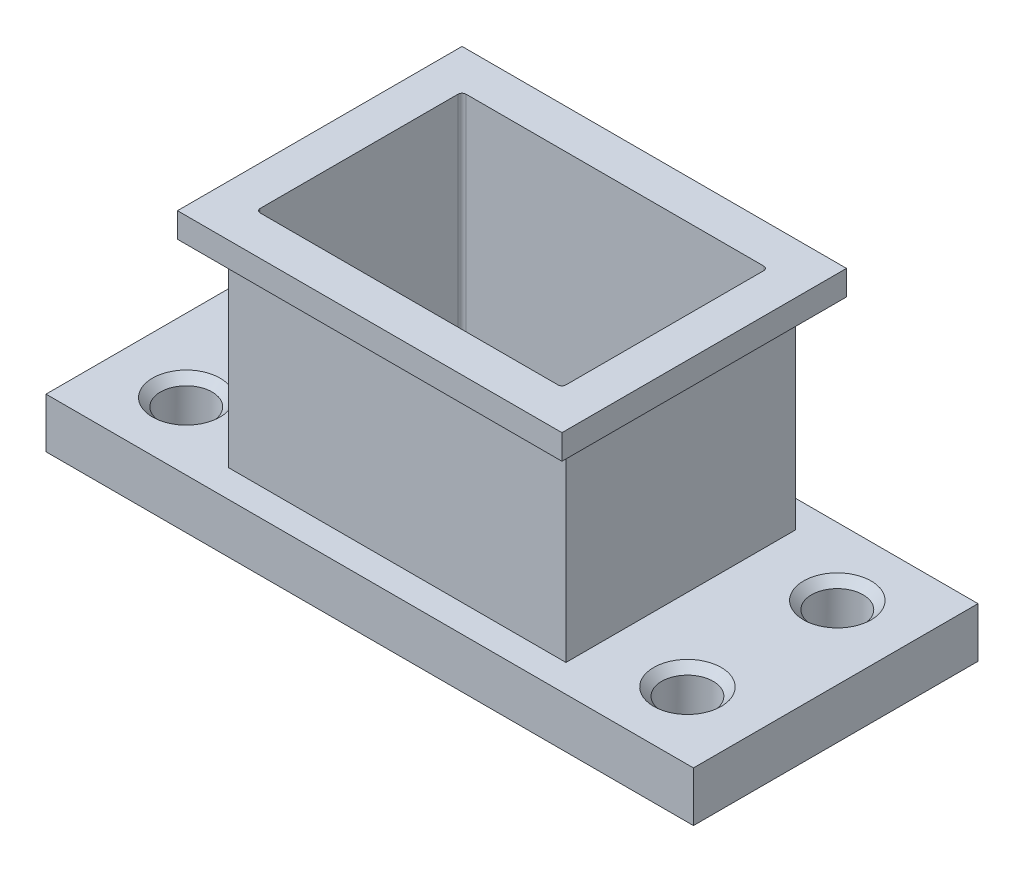
SolidWorks part; units mm, degrees
ref_plane "Front Plane" through (0, 0, 0) normal (0, 0, 1) x (1, 0, 0)
ref_plane "Top Plane" through (0, 0, 0) normal (0, 1, 0) x (1, 0, 0)
ref_plane "Right Plane" through (0, 0, 0) normal (1, 0, 0) x (0, 0, -1)
sketch "Sketch1" plane through (0, 0, 0) normal (0, 1, 0) x (1, 0, 0)
  line L1 (0, 0) -> (41.148, 0)
  line L2 (0, 0) -> (0, 18.0848)
  line L3 (0, 18.0848) -> (41.148, 18.0848)
  line L4 (41.148, 0) -> (41.148, 18.0848)
  line L5 (10.8585, 15.5829) -> (30.2895, 15.5829)
  line L6 (10.8585, 15.5829) -> (10.8585, 2.5019)
  line L7 (10.8585, 2.5019) -> (30.2895, 2.5019)
  line L8 (30.2895, 15.5829) -> (30.2895, 2.5019)
  dimension "D1" = 18.0848
  dimension "D2" = 41.148
  dimension "D3" = 10.8585
  dimension "D4" = 2.5019
  dimension "D5" = 2.5019
  dimension "D6" = 10.8585
  dimension "D7" = 19.431
  dimension "D8" = 13.081
extrude "Extrude1" add sketch "Sketch1" along normal blind 17.4498
sketch "Sketch2" plane through (0, 17.4498, 0) normal (0, 1, 0) x (-1, 0, 0)
  line L1 (0, 0) -> (-41.148, 0) construction
  line L2 (0, -18.0848) -> (-8.3566, -18.0848)
  line L3 (0, -18.0848) -> (0, 0)
  line L4 (0, 0) -> (-8.3566, 0)
  line L5 (-8.3566, -18.0848) -> (-8.3566, 0)
  line L7 (-41.148, -18.0848) -> (-32.7914, -18.0848)
  line L8 (-41.148, -18.0848) -> (-41.148, 0)
  line L9 (-41.148, 0) -> (-32.7914, 0)
  line L10 (-32.7914, -18.0848) -> (-32.7914, 0)
  dimension "D2" = 8.3566
  dimension "D1" = 8.3566
  dimension "D3" = 24.4348
extrude "Cut-Extrude1" cut sketch "Sketch2" against normal blind 14.2748
sketch "Sketch3" plane through (0, 17.4498, 0) normal (0, 1, 0) x (-1, 0, 0)
  line L1 (-31.2928, -16.3322) -> (-9.8552, -16.3322)
  line L2 (-31.2928, -16.3322) -> (-31.2928, -1.7526)
  line L3 (-31.2928, -1.7526) -> (-9.8552, -1.7526)
  line L4 (-8.3566, 0) -> (-32.7914, 0)
  line L5 (-32.7914, 0) -> (-32.7914, -18.0848)
  line L6 (-32.7914, -18.0848) -> (-8.3566, -18.0848)
  line L7 (-8.3566, -18.0848) -> (-8.3566, 0)
  line L8 (-8.3566, 0) -> (-32.7914, 0)
  line L9 (-32.7914, 0) -> (-32.7914, -18.0848)
  line L10 (-32.7914, -18.0848) -> (-8.3566, -18.0848)
  line L11 (-8.3566, -18.0848) -> (-8.3566, 0)
  line L12 (-9.8552, -16.3322) -> (-9.8552, -1.7526)
  dimension "D2" = 1.4986
  dimension "D3" = 1.4986
  dimension "D4" = 21.4376
  dimension "D5" = 1.7526
  dimension "D6" = 1.7526
  dimension "D7" = 14.5796
  dimension "D1" = 0
extrude "Cut-Extrude2" cut sketch "Sketch3" against normal up to surface (12.7 mm away) from offset 1.5748 up to face at (36.9697, 3.175, -9.0424) offset against normal yes
sketch "Sketch4" plane through (0, 3.175, 0) normal (0, 1, 0) x (-1, 0, 0)
  line L0 (0, -18.0848) -> (0, 0) construction
  line L1 (0, 0) -> (-41.148, 0) construction
  line L2 (-41.148, -18.0848) -> (0, -18.0848) construction
  line L3 (-41.148, 0) -> (-41.148, -18.0848) construction
  circle A0 centre (-36.4998, -13.7922) radius 1.6383
  circle A1 centre (-36.4998, -4.2672) radius 1.6383
  circle A2 centre (-4.6482, -4.2672) radius 1.6383
  circle A3 centre (-4.6482, -13.7922) radius 1.6383
  dimension "D1" = 3.2766
  dimension "D2" = 4.2926
  dimension "D3" = 4.6482
  dimension "D5" = 4.2672
  dimension "D6" = 31.8516
  dimension "D7" = 9.525
  dimension "D4" = 4.6482
extrude "Cut-Extrude3" cut sketch "Sketch4" against normal through all
chamfer "Chamfer1" distance 0.508 angle 45 4 edges at (4.6482, 3.175, -12.1539) (4.6482, 3.175, -2.6289) (36.4998, 3.175, -2.6289) (36.4998, 3.175, -12.1539)
fillet "Fillet1" radius 0.254 4 edges at (10.8585, 8.7249, -15.5829) (10.8585, 8.7249, -2.5019) (30.2895, 8.7249, -2.5019) (30.2895, 8.7249, -15.5829)
chamfer "Chamfer2" distance 0.508 angle 45 4 edges at (4.6482, 0, -2.6289) (4.6482, 0, -12.1539) (36.4998, 0, -12.1539) (36.4998, 0, -2.6289)
